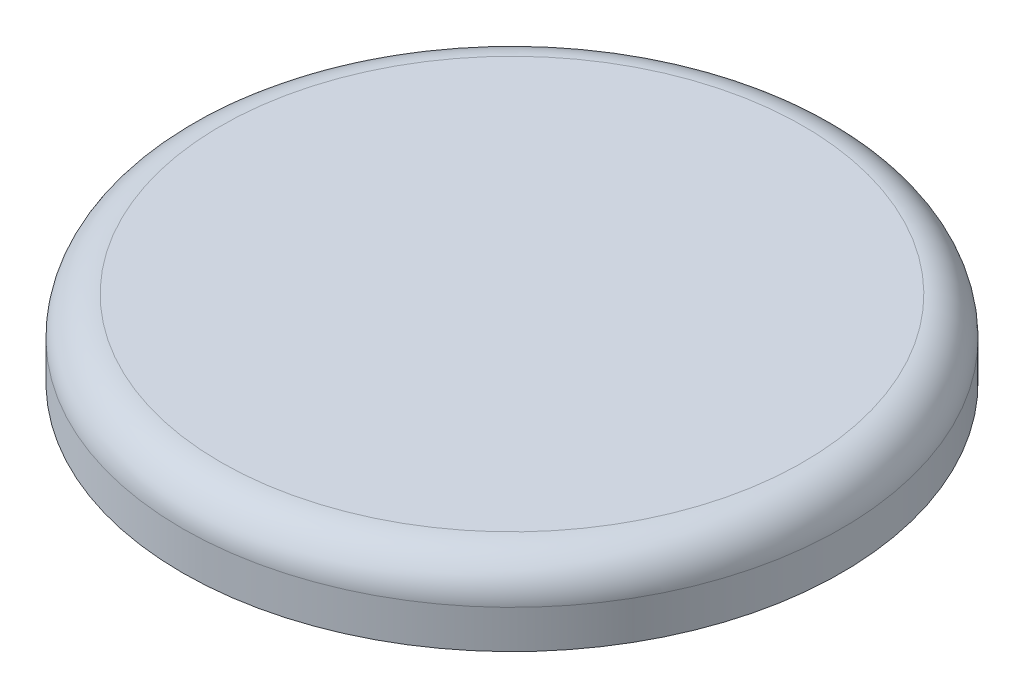
SolidWorks part; units mm, degrees
ref_plane "Front Plane" through (0, 0, 0) normal (0, 0, 1) x (1, 0, 0)
ref_plane "Top Plane" through (0, 0, 0) normal (0, 1, 0) x (1, 0, 0)
ref_plane "Right Plane" through (0, 0, 0) normal (1, 0, 0) x (0, 0, -1)
sketch "Sketch1" plane through (0, 0, 0) normal (0, 1, 0) x (1, 0, 0)
  circle A0 centre (0, 0) radius 8.6
extrude "Boss-Extrude1" add sketch "Sketch1" along normal blind 2
fillet "Fillet1" radius 1 1 edges at (0, 2, 8.6)
shell "Shell1" thickness 0.2
